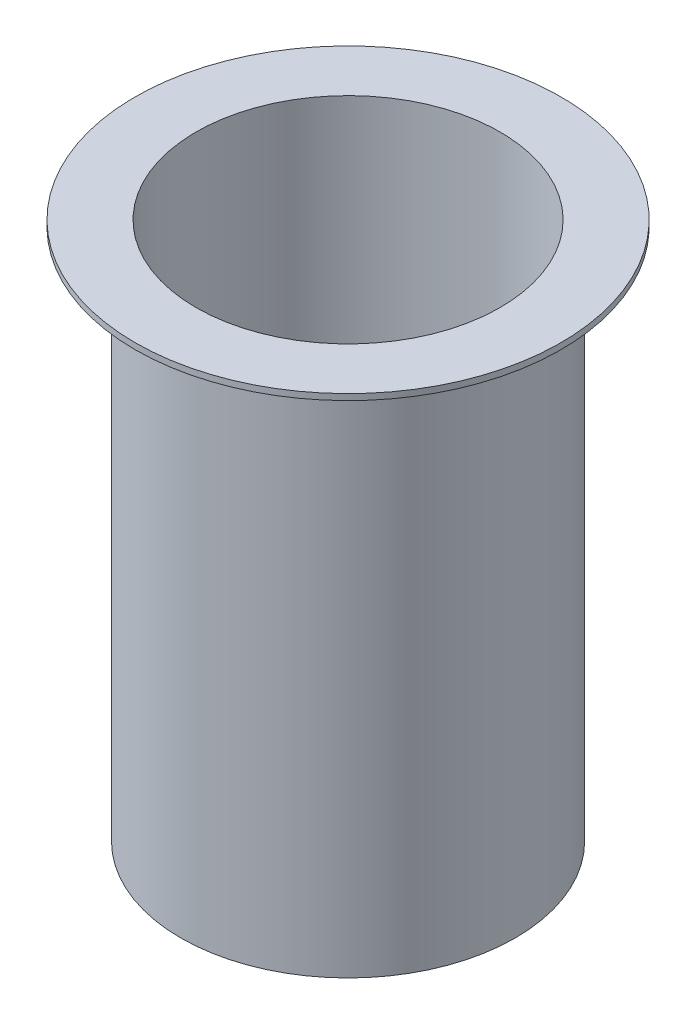
SolidWorks part; units mm, degrees
ref_plane "Alzado" through (0, 0, 0) normal (0, 0, 1) x (1, 0, 0)
ref_plane "Planta" through (0, 0, 0) normal (0, 1, 0) x (1, 0, 0)
ref_plane "Vista lateral" through (0, 0, 0) normal (1, 0, 0) x (0, 0, -1)
sketch "Croquis1" plane through (0, 0, 0) normal (0, 1, 0) x (1, 0, 0)
  circle A0 centre (0, 0) radius 50
  circle A1 centre (0, 0) radius 55
  dimension "D1" = 100
  dimension "D2" = 110
extrude "Saliente-Extruir1" add sketch "Croquis1" against normal blind 177
sketch "Croquis2" plane through (0, 0, 0) normal (0, 1, 0) x (1, 0, 0)
  circle A0 centre (0, 0) radius 70
  circle A1 centre (0, 0) radius 50 construction
  circle A2 centre (0, 0) radius 50
  dimension "D1" = 140
extrude "Saliente-Extruir2" add sketch "Croquis2" against normal blind 2
